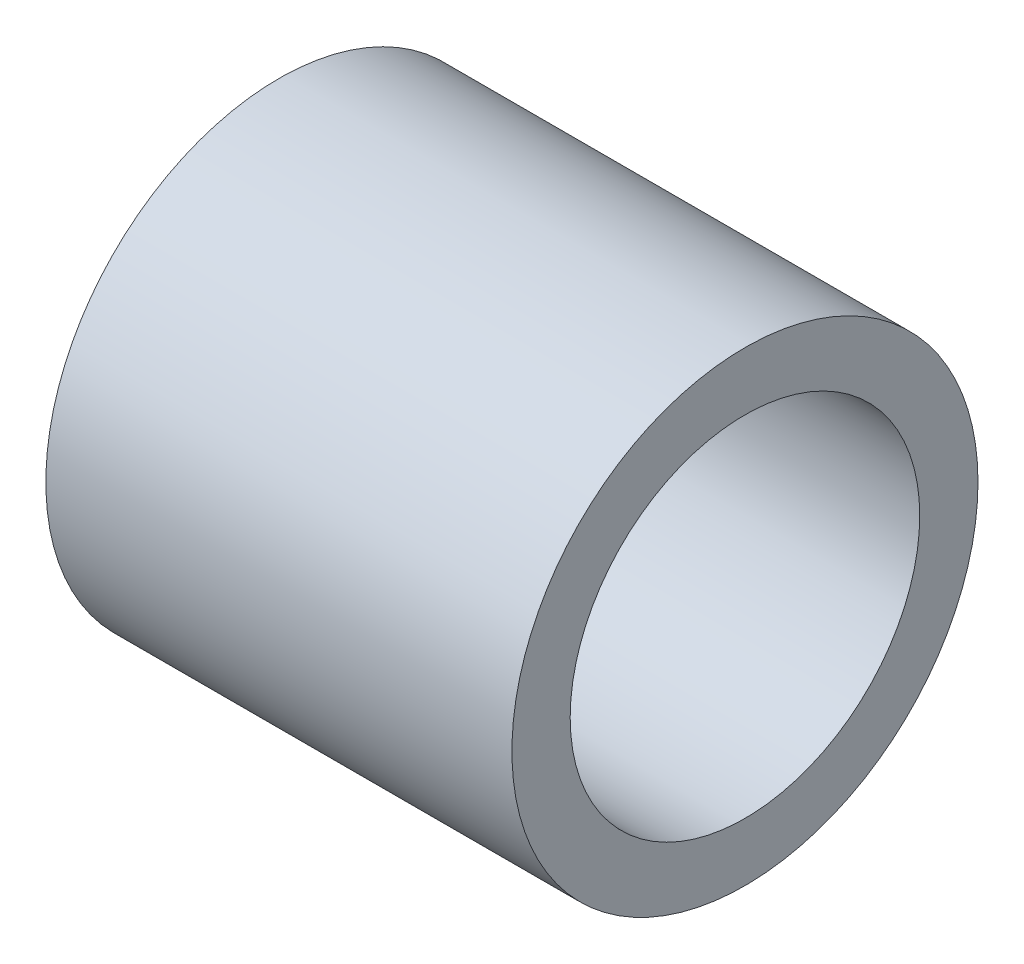
SolidWorks part; units mm, degrees
ref_plane "Front Plane" through (0, 0, 0) normal (0, 0, 1) x (1, 0, 0)
ref_plane "Top Plane" through (0, 0, 0) normal (0, 1, 0) x (1, 0, 0)
ref_plane "Right Plane" through (0, 0, 0) normal (1, 0, 0) x (0, 0, -1)
sketch "Sketch1" plane through (0, 0, 0) normal (1, 0, 0) x (0, 0, -1)
  circle A0 centre (0, 0) radius 9.525
  circle A1 centre (0, 0) radius 12.7
  dimension "D1" = 25.4
  dimension "D2" = 19.05
extrude "Boss-Extrude1" add sketch "Sketch1" along normal mid plane 25.4
